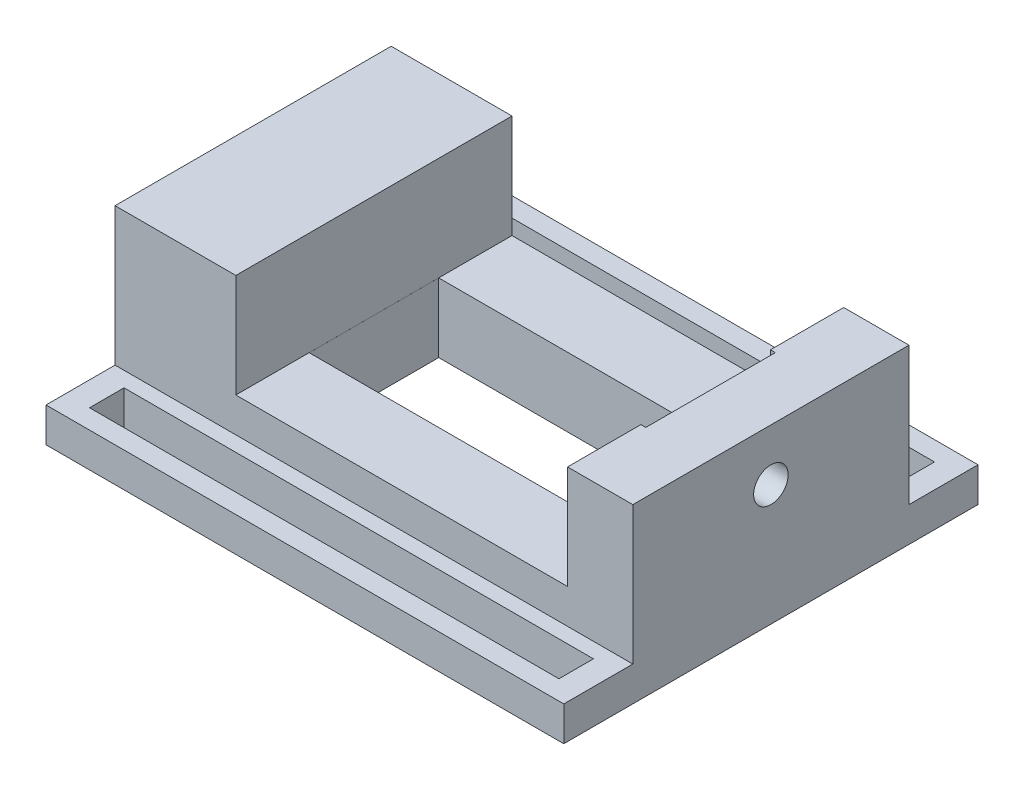
SolidWorks part; units mm, degrees
ref_plane "Спереди" through (0, 0, 0) normal (0, 0, 1) x (1, 0, 0)
ref_plane "Сверху" through (0, 0, 0) normal (0, 1, 0) x (1, 0, 0)
ref_plane "Справа" through (0, 0, 0) normal (1, 0, 0) x (0, 0, -1)
sketch "Эскиз1" plane through (0, 0, 0) normal (0, 1, 0) x (1, 0, 0)
  line L1 (-75, 40) -> (75, 40)
  line L2 (-75, 40) -> (-75, -40)
  line L3 (-75, -40) -> (75, -40)
  line L4 (75, 40) -> (75, -40)
  line L5 (-75, 40) -> (75, -40) construction
  line L6 (-75, -40) -> (75, 40) construction
  point P0 (0, 0)
extrude "Бобышка-Вытянуть1" add sketch "Эскиз1" along normal blind 40
sketch "Эскиз2" plane through (0, 0, 0) normal (0, -1, 0) x (1, 0, 0)
  line L0 (-75, 0) -> (75, 0) construction
  line L1 (75, -60) -> (-75, -60)
  line L2 (75, -60) -> (75, 60)
  line L3 (75, 60) -> (-75, 60)
  line L4 (-75, -60) -> (-75, 60)
  line L5 (75, -60) -> (-75, 60) construction
  line L6 (75, 60) -> (-75, -60) construction
  line L7 (-67.9915, 44.3932) -> (67.9915, 44.3932)
  line L8 (-67.9915, 44.3932) -> (-67.9915, 54.3932)
  line L9 (-67.9915, 54.3932) -> (67.9915, 54.3932)
  line L10 (67.9915, 44.3932) -> (67.9915, 54.3932)
  line L11 (67.9915, -44.3932) -> (67.9915, -54.3932)
  line L12 (-67.9915, -54.3932) -> (67.9915, -54.3932)
  line L13 (-67.9915, -44.3932) -> (-67.9915, -54.3932)
  line L14 (-67.9915, -44.3932) -> (67.9915, -44.3932)
  point P0 (0, 0)
extrude "Бобышка-Вытянуть2" add sketch "Эскиз2" along normal blind 10
sketch "Эскиз3" plane through (0, 0, 40) normal (0, 0, 1) x (1, 0, 0)
  line L0 (-75, 40) -> (75, 40) construction
  line L1 (-40, 40) -> (56.093, 40)
  line L2 (-40, 40) -> (-40, 10)
  line L3 (-40, 10) -> (56.093, 10)
  line L4 (56.093, 40) -> (56.093, 10)
extrude "Вырез-Вытянуть1" cut sketch "Эскиз3" against normal through all
sketch "Эскиз5" plane through (0, -10, 0) normal (0, -1, 0) x (1, 0, 0)
  line L0 (-75, 0) -> (75, 0) construction
  line L2 (-39.995, 18.7674) -> (-39.995, -18.7674)
  line L3 (-39.995, -18.7674) -> (57.5152, -18.7674)
  line L4 (57.5152, 18.7674) -> (57.5152, -18.7674)
  line L5 (-75, 60) -> (-75, -60) construction
  line L6 (75, -60) -> (75, 60) construction
  line L7 (-39.995, 18.7674) -> (57.5152, 18.7674)
  point P0 (0, 0)
  point P15 (57.5152, 0)
  point P16 (-39.995, 0)
extrude "Вырез-Вытянуть2" cut sketch "Эскиз5" against normal through all
sketch "Эскиз6" plane through (75, 0, 0) normal (1, 0, 0) x (0, 0, -1)
  line L0 (0, 40) -> (0, -10) construction
  line L1 (-40, 40) -> (40, 40) construction
  line L2 (60, -10) -> (-60, -10) construction
  circle A0 centre (0, 25) radius 5
extrude "Вырез-Вытянуть3" cut sketch "Эскиз6" against normal blind 30
